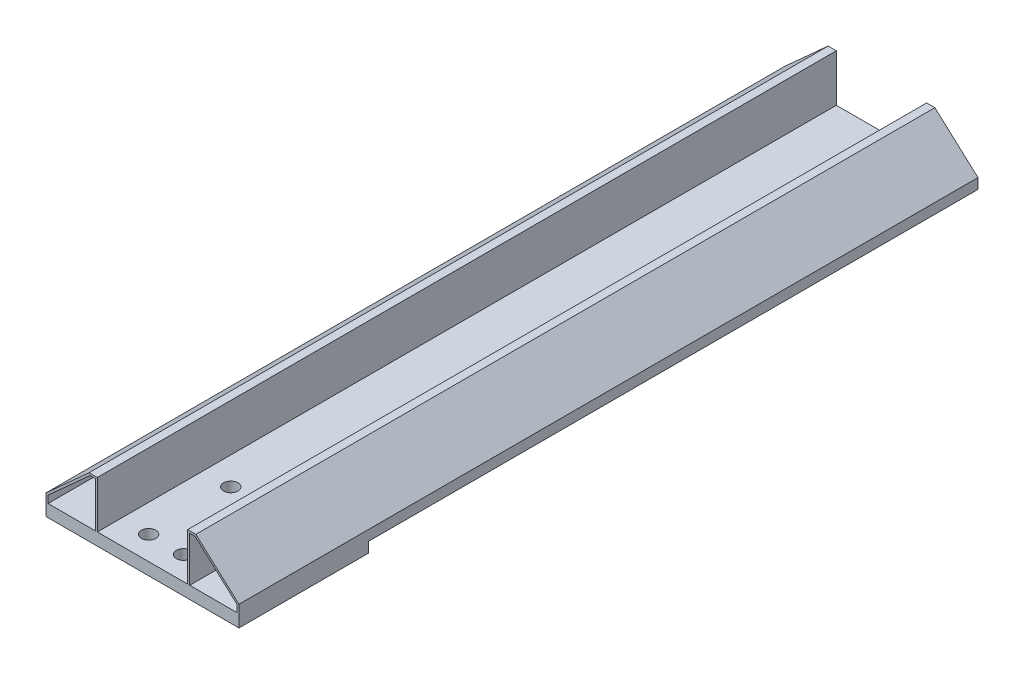
SolidWorks part; units mm, degrees
material "Aleación 1060"
ref_plane "Alzado" through (0, 0, 0) normal (0, 0, 1) x (1, 0, 0)
ref_plane "Planta" through (0, 0, 0) normal (0, 1, 0) x (1, 0, 0)
ref_plane "Vista lateral" through (0, 0, 0) normal (1, 0, 0) x (0, 0, -1)
sketch "Croquis2" plane through (0, 0, 0) normal (0, 0, 1) x (1, 0, 0)
  line L1 (0, 0) -> (94, 0)
  line L2 (0, 0) -> (0, -24)
  line L3 (0, -24) -> (94, -24)
  line L4 (94, 0) -> (94, -24)
  dimension "D1" = 94
  dimension "D2" = 24
extrude "Saliente-Extruir1" add sketch "Croquis2" along normal blind 360
sketch "Croquis4" plane through (0, 0, 0) normal (0, 0, -1) x (-1, 0, 0)
  line L0 (-94, -24) -> (-69, -24)
  line L1 (0, -24) -> (-94, -24) construction
  line L2 (0, -24) -> (-25, -24)
  line L3 (-69, -24) -> (-69, 0)
  line L4 (-94, 0) -> (0, 0) construction
  line L5 (-25, -24) -> (-25, 0)
  line L6 (-94, -24) -> (-94, -19)
  line L7 (-94, -24) -> (-94, 0) construction
  line L8 (0, -24) -> (0, -19)
  line L9 (0, 0) -> (0, -24) construction
  line L10 (-69, 0) -> (-73, 0)
  line L11 (-25, 0) -> (-21, 0)
  line L12 (-73, 0) -> (-94, -19)
  line L13 (-94, -19) -> (-94, 0)
  line L14 (-94, 0) -> (-73, 0)
  line L15 (-21, 0) -> (0, -19)
  line L16 (0, -19) -> (0, 0)
  line L17 (0, 0) -> (-21, 0)
  line L18 (-69, 0) -> (-25, 0)
  line L19 (-94, -24) -> (-94, -23)
  line L20 (0, -24) -> (0, -23)
  line L21 (0, -23) -> (-94, -23)
  line M3 (0, -24) -> (0, 0)
  line M4 (0, 0) -> (-94, 0)
  line M5 (-94, 0) -> (-94, -24)
extrude "Cortar-Extruir2" cut sketch "Croquis4" against normal blind 360 contours L12 M4 M5 | L21 L5 L3 M4 | L15 M4 M3
sketch "Croquis6" plane through (0, 0, 0) normal (0, 0, -1) x (-1, 0, 0)
  line L0 (-69, 0) -> (-69, -24)
  line L1 (0, -24) -> (-94, -24) construction
  line L2 (-25, 0) -> (-25, -24)
  line L3 (-94, -24) -> (-69, -24)
  line L4 (-25, -24) -> (0, -24)
  line L9 (-70, 0) -> (-70, -23)
  line L10 (-93, -19.4438) -> (-93, -24)
  line L11 (-72.3291, -0.7415) -> (-93, -19.4438)
  line L12 (-93, -19.4438) -> (-93, -24)
  line L13 (-72.3291, -0.7415) -> (-93, -19.4438)
  line L14 (-73, -1) -> (-69, -1)
  line L15 (-73, -1) -> (-69, -1)
  line L16 (-94, -23) -> (-70, -23)
  line L17 (-24, 0) -> (-24, -24)
  line L24 (-25, -23) -> (0, -23)
  line L25 (-94, -23) -> (-69, -23)
  line L26 (-69, -23) -> (-70, -23)
  line L27 (-1, -19.4438) -> (-1, -24)
  line L28 (-21.3852, -1) -> (-1, -19.4438)
  line L29 (-25, -1) -> (-21.3852, -1)
  line L30 (-1, -19.4438) -> (-1, -24)
  line L31 (-21.3852, -1) -> (-1, -19.4438)
  line L32 (-25, -1) -> (-21.3852, -1)
  line L33 (-69, -1) -> (-73, -1)
  line L34 (-72.3291, -0.7415) -> (-93, -19.4438)
  line L35 (-93, -24) -> (-93, -19.4438)
  line L36 (-70, -23) -> (-94, -23)
  dimension "D1" = 1
  dimension "D2" = 1
  dimension "D3" = 1
  dimension "D4" = 1
  dimension "D5" = 1
  dimension "D6" = 1
extrude "Cortar-Extruir3" cut sketch "Croquis6" against normal blind 360 contours L12 L16 L9 L15 L13
sketch "Croquis7" plane through (0, 0, 0) normal (0, 0, -1) x (-1, 0, 0)
  line L10 (-25, 0) -> (-25, -24)
  line L11 (0, -24) -> (-94, -24) construction
  line L12 (-25, -24) -> (0, -24)
  line L13 (0, -24) -> (0, -19)
  line L14 (0, -19) -> (-21, 0)
  line L15 (-21, 0) -> (-25, 0)
  line L16 (-24, -1) -> (-24, -23)
  line L17 (-24, -23) -> (-1, -23)
  line L18 (-1, -23) -> (-1, -19.4438)
  line L19 (-1, -19.4438) -> (-21.3852, -1)
  line L20 (-21.3852, -1) -> (-24, -1)
  line L21 (-24, -1) -> (-21.3852, -1)
  line L22 (-1, -19.4438) -> (-1, -23)
  line L23 (-24, -23) -> (-24, -1)
  dimension "D1" = 1
extrude "Cortar-Extruir5" cut sketch "Croquis7" against normal blind 360 contours L19 L20 L16 L17 L18
sketch "Croquis8" plane through (0, -24, 0) normal (0, -1, 0) x (1, 0, 0)
  line L0 (0, 360) -> (94, 360) construction
  line L1 (0, 360) -> (94, 360)
  line L2 (0, 360) -> (0, 297)
  line L3 (0, 297) -> (94, 297)
  line L4 (94, 360) -> (94, 297)
  line L5 (0, 360) -> (0, 0) construction
  line L6 (94, 360) -> (94, 0) construction
  dimension "D1" = 63
extrude "Saliente-Extruir2" add sketch "Croquis8" along normal blind 5
sketch "Croquis9" plane through (0, -29, 0) normal (0, -1, 0) x (1, 0, 0)
  circle A0 centre (38.5, 348.5) radius 3.5
  circle A1 centre (55.5, 348.5) radius 3.5
  circle A2 centre (38.5, 308.5) radius 3.5
  circle A3 centre (55.5, 308.5) radius 3.5
extrude "Cortar-Extruir6" cut sketch "Croquis9" against normal through all
